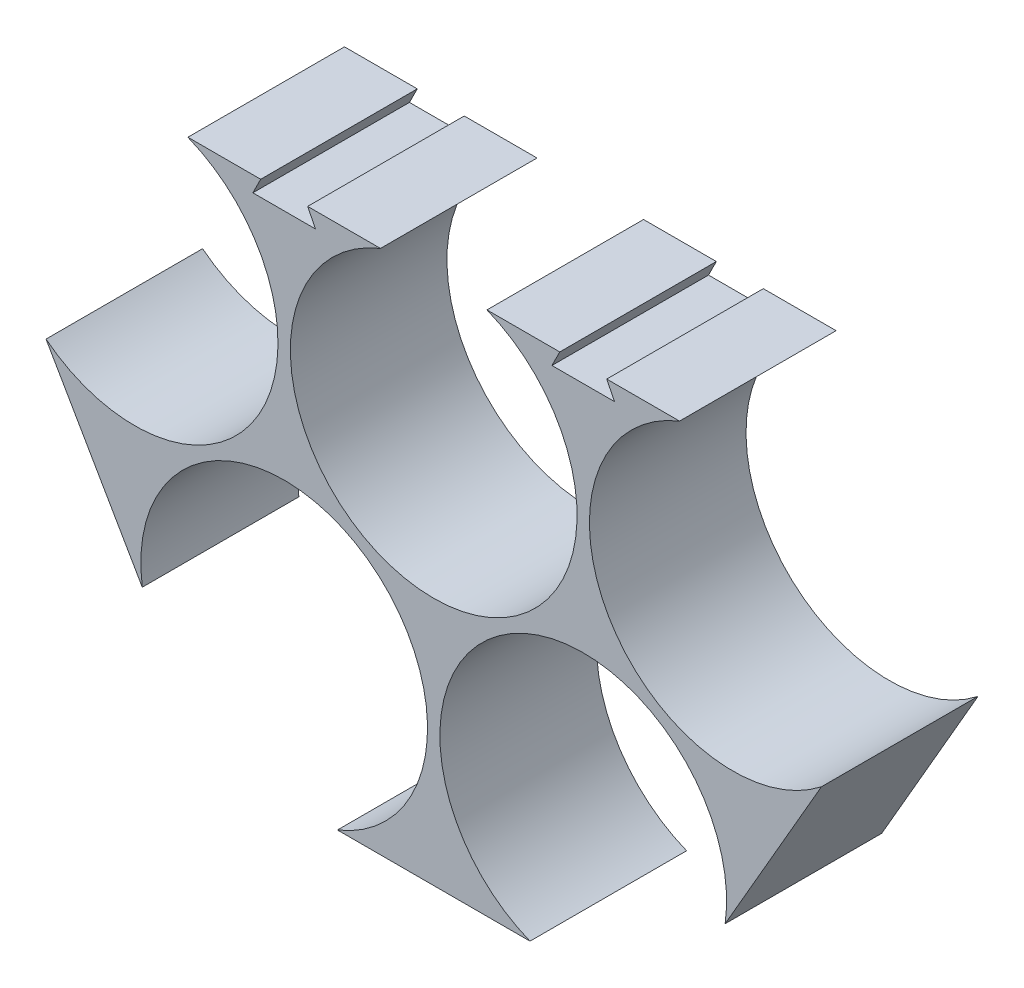
SolidWorks part; units mm, degrees
ref_plane "Front Plane" through (0, 0, 0) normal (0, 0, 1) x (1, 0, 0)
ref_plane "Top Plane" through (0, 0, 0) normal (0, 1, 0) x (1, 0, 0)
ref_plane "Right Plane" through (0, 0, 0) normal (1, 0, 0) x (0, 0, -1)
sketch "Sketch4" plane through (0, 0, 0) normal (0, 0, 1) x (1, 0, 0)
  line L0 (-41.6472, -7.1553) -> (-32.0972, -23.6963)
  line L1 (-32.0972, -23.6963) -> (-22.5472, -7.1553)
  line L2 (-22.5472, -7.1553) -> (-12.9972, -23.6963)
  line L3 (-12.9972, -23.6963) -> (-3.4472, -7.1553)
  line L4 (-50.7907, 5.0735) -> (9.2093, 5.0735)
  line L5 (-41.6472, -7.1553) -> (-22.5472, -7.1553)
  line L6 (-22.5472, -7.1553) -> (-3.4472, -7.1553)
  line L7 (-12.9972, -7.1553) -> (-12.9972, 1.3447)
  line L8 (-32.0972, -23.6963) -> (-12.9972, -23.6963)
  line L9 (-22.5472, -23.6963) -> (-22.5472, -32.1963)
  line L10 (-32.0972, -7.1553) -> (-32.0972, 1.3447)
  line L11 (-38.2466, 1.3447) -> (-25.9478, 1.3447)
  line L12 (-19.1466, 1.3447) -> (-6.8478, 1.3447)
  line L13 (-16.3978, -32.1963) -> (-28.6966, -32.1963)
  line L14 (-36.8722, -15.4258) -> (-44.2334, -19.6758)
  line L15 (-8.2222, -15.4258) -> (-0.861, -19.6758)
  line L16 (-3.9357, -25.0014) -> (2.2137, -14.3503)
  line L17 (-41.1587, -25.0014) -> (-47.3081, -14.3503)
  circle A0 centre (-41.6472, -7.1553) radius 9.155
  circle A1 centre (-22.5472, -7.1553) radius 9.155
  circle A2 centre (-32.0972, -23.6963) radius 9.155
  circle A3 centre (-12.9972, -23.6963) radius 9.155
  circle A4 centre (-3.4472, -7.1553) radius 9.155
  point P21 (-32.0972, 1.3447)
  point P24 (-12.9972, 1.3447)
  point P27 (-22.5472, -32.1963)
  point P34 (-0.861, -19.6758)
  point P37 (-44.2334, -19.6758)
  dimension "D1" = 18.31
  dimension "D2" = 18.31
  dimension "D3" = 18.31
  dimension "D4" = 18.31
  dimension "D5" = 18.31
  dimension "D6" = 19.1
  dimension "D7" = 19.1
  dimension "D8" = 19.1
  dimension "D9" = 19.1
  dimension "D10" = 60
  dimension "D11" = 60
  dimension "D12" = 8.5
  dimension "D13" = 8.5
  dimension "D14" = 8.5
  dimension "D15" = 8.5
  dimension "D16" = 8.5
extrude "Boss-Extrude1" add sketch "Sketch4" along normal blind 10 contours A0 L17 L14 L0 | A2 L0 L14 L17 | A2 L1 A1 L5 A0 L0 | A0 L5 L10 L11 | A1 L11 L10 L5 | A3 L2 A1 L1 A2 L8 | A2 L13 L9 L8 | A3 L8 L9 L13 | A4 L6 A1 L2 A3 L3 | A1 L6 L7 L12 | A4 L12 L7 L6 | A3 L16 L15 L3 | A4 L3 L15 L16
sketch "Sketch5" plane through (0, 0, 0) normal (0, 0, -1) x (-1, 0, 0)
  line L0 (10.9972, 0.3447) -> (14.9972, 0.3447)
  line L1 (11.4972, 1.3447) -> (14.4972, 1.3447)
  line L2 (12.9972, 1.3447) -> (12.9972, 0.3447)
  line L3 (32.0972, 1.3447) -> (32.0972, 0.3447)
  line L4 (30.0972, 0.3447) -> (34.0972, 0.3447)
  line L5 (19.1466, 1.3447) -> (6.8478, 1.3447) construction
  line L6 (30.5972, 1.3447) -> (33.5972, 1.3447)
  line L7 (38.2466, 1.3447) -> (25.9478, 1.3447) construction
  line L8 (14.9972, 0.3447) -> (14.4972, 1.3447)
  line L9 (10.9972, 0.3447) -> (11.4972, 1.3447)
  line L10 (30.0972, 0.3447) -> (30.5972, 1.3447)
  line L11 (34.0972, 0.3447) -> (33.5972, 1.3447)
  point P5 (12.9972, 0.3447)
  point P15 (32.0972, 0.3447)
  point P19 (12.9972, 1.3447)
  point P24 (32.0972, 1.3447)
  line M8 (38.2466, 1.3447) -> (25.9478, 1.3447)
  line M10 (19.1466, 1.3447) -> (6.8478, 1.3447)
extrude "Cut-Extrude1" cut sketch "Sketch5" against normal through all contours L0 L8 L2 M10 | L9 L0 L2 L1 | L10 L4 L3 M8 | L4 L11 L3 M8
